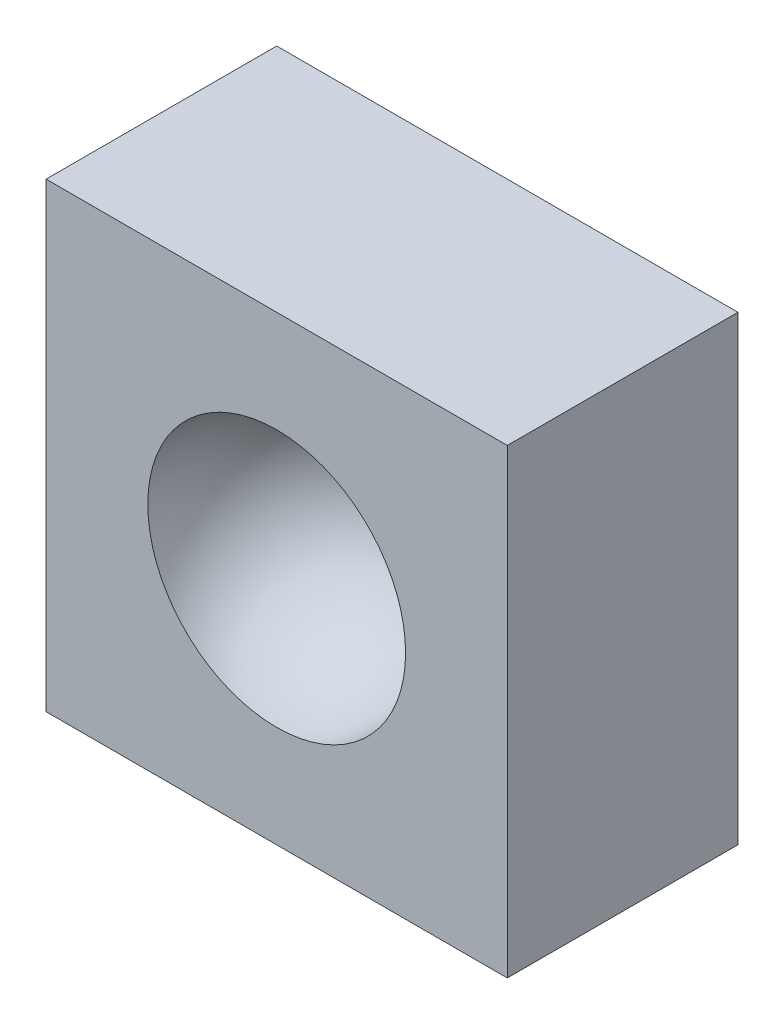
SolidWorks part; units mm, degrees
ref_plane "Plano frontal" through (0, 0, 0) normal (0, 0, 1) x (1, 0, 0)
ref_plane "Plano superior" through (0, 0, 0) normal (0, 1, 0) x (1, 0, 0)
ref_plane "Plano direito" through (0, 0, 0) normal (1, 0, 0) x (0, 0, -1)
sketch "Esboço1" plane through (0, 0, 0) normal (0, 0, 1) x (1, 0, 0)
  line L1 (-50, 50) -> (50, 50)
  line L2 (-50, 50) -> (-50, -50)
  line L3 (-50, -50) -> (50, -50)
  line L4 (50, 50) -> (50, -50)
  line L5 (-50, 50) -> (50, -50) construction
  line L6 (-50, -50) -> (50, 50) construction
  point P0 (0, 0)
  dimension "D1" = 100
  dimension "D2" = 100
extrude "Extrusão1" add sketch "Esboço1" along normal blind 50
sketch "Esboço2" plane through (0, 0, 50) normal (0, 0, 1) x (1, 0, 0)
  line L0 (-27.9454, 0) -> (27.9454, 0)
  arc A0 (27.9454, 0) -> (-27.9454, 0) centre (0, 0) ccw
revolve "Corte-Revolução1" cut sketch "Esboço2" angle 360 about L0
